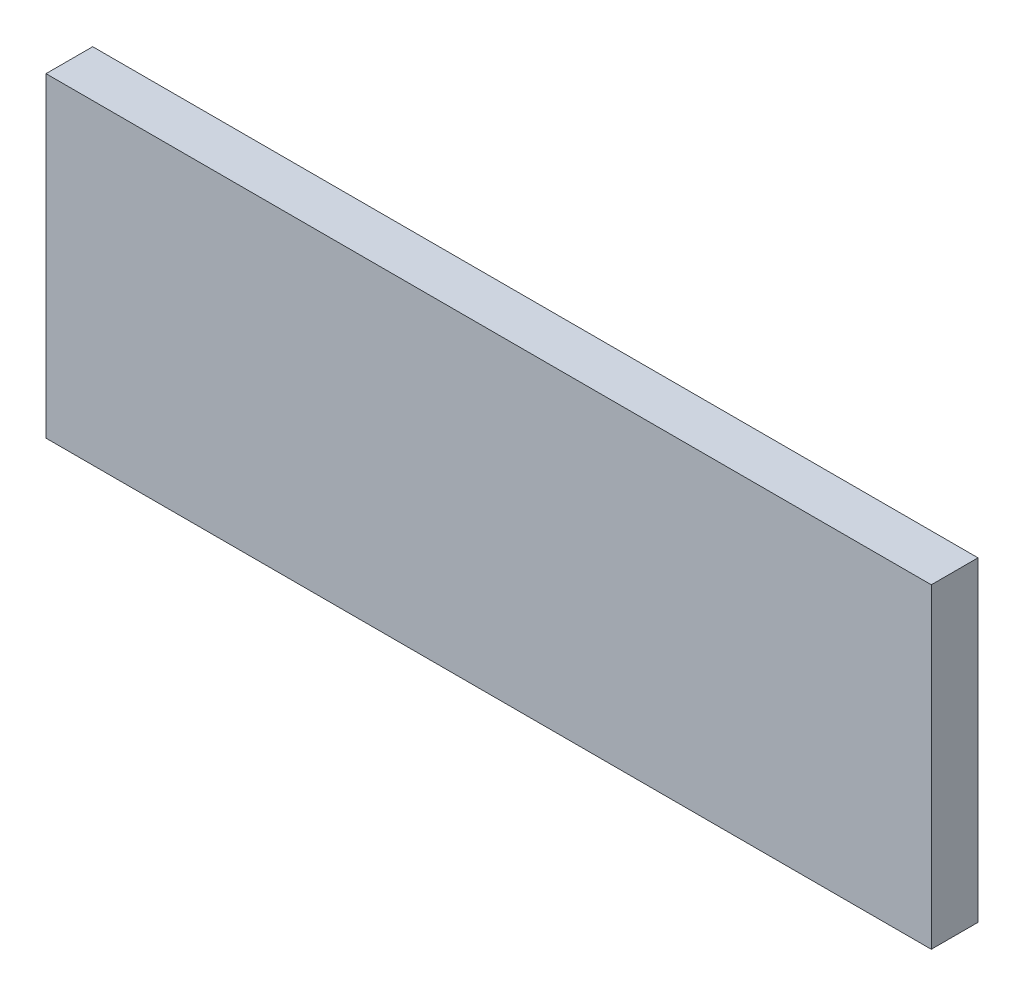
SolidWorks part; units mm, degrees
other "Caméra1" [suppressed]
material "Erable"
ref_plane "Plan1" through (0, 0, 0) normal (0, 0, 1) x (1, 0, 0)
ref_plane "Plan2" through (0, 0, 0) normal (0, 1, 0) x (1, 0, 0)
ref_plane "Plan3" through (0, 0, 0) normal (1, 0, 0) x (0, 0, -1)
sketch "Esquisse1" plane through (0, 0, 0) normal (0, 0, 1) x (1, 0, 0)
  line L1 (-142.1712, 50.7) -> (142.1712, 50.7)
  line L2 (-142.1712, 50.7) -> (-142.1712, -50.7)
  line L3 (-142.1712, -50.7) -> (142.1712, -50.7)
  line L4 (142.1712, 50.7) -> (142.1712, -50.7)
  line L5 (-142.1712, 50.7) -> (142.1712, -50.7) construction
  line L6 (-142.1712, -50.7) -> (142.1712, 50.7) construction
  point P0 (0, 0)
extrude "Boss.-Extru.1" add sketch "Esquisse1" along normal blind 15
